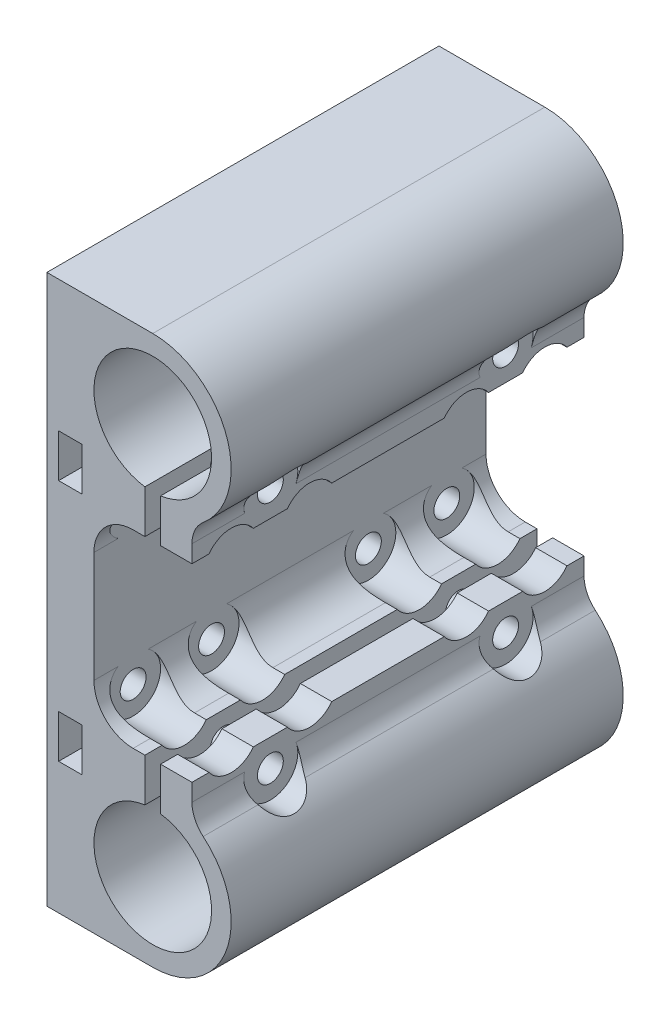
SolidWorks part; units mm, degrees
ref_plane "Plano frontal" through (0, 0, 0) normal (0, 0, 1) x (1, 0, 0)
ref_plane "Plano superior" through (0, 0, 0) normal (0, 1, 0) x (1, 0, 0)
ref_plane "Plano direito" through (0, 0, 0) normal (1, 0, 0) x (0, 0, -1)
sketch "Esboço1" plane through (0, 0, 0) normal (0, 0, 1) x (1, 0, 0)
  line L0 (0, 0) -> (67.7245, 0) construction
  line L1 (0, 35) -> (0, -35)
  line L2 (0, -35) -> (13.5, -35)
  line L3 (18.5, 14.2762) -> (18.5, 12.067)
  line L4 (18.5, 12.067) -> (14.5, 12.067)
  line L5 (12.5, -12.067) -> (11, -12.067)
  line L6 (6, -7.067) -> (6, 7.067)
  line L7 (12.5, -17.567) -> (12.5, -12.067)
  line L8 (14.5, 12.067) -> (14.5, 17.567)
  line L9 (12.5, 17.567) -> (12.5, 12.067)
  line L10 (13.5, 35) -> (0, 35)
  line L11 (12.5, 12.067) -> (11, 12.067)
  line L12 (14.5, -12.067) -> (14.5, -17.567)
  line L13 (18.5, -12.067) -> (14.5, -12.067)
  line L14 (18.5, -14.2762) -> (18.5, -12.067)
  line L15 (13.5, 25) -> (13.5, 21.6715) construction
  line L16 (4.5, -18.25) -> (1.5, -12.75) construction
  line L17 (4.5, 12.75) -> (1.5, 12.75)
  line L18 (4.5, 12.75) -> (4.5, 18.25)
  line L19 (4.5, 18.25) -> (1.5, 18.25)
  line L20 (1.5, 12.75) -> (1.5, 18.25)
  line L21 (4.5, 12.75) -> (1.5, 18.25) construction
  line L22 (4.5, 18.25) -> (1.5, 12.75) construction
  line L23 (4.5, -12.75) -> (1.5, -18.25) construction
  line L24 (1.5, -12.75) -> (1.5, -18.25)
  line L25 (4.5, -18.25) -> (1.5, -18.25)
  line L26 (4.5, -12.75) -> (4.5, -18.25)
  line L27 (4.5, -12.75) -> (1.5, -12.75)
  arc A0 (14.5, 17.567) -> (12.5, 17.567) centre (13.5, 25) ccw
  arc A1 (19.9286, -17.3401) -> (13.5, -35) centre (13.5, -25) cw
  arc A2 (19.9286, 17.3401) -> (13.5, 35) centre (13.5, 25) ccw
  arc A3 (14.5, -17.567) -> (12.5, -17.567) centre (13.5, -25) cw
  arc A4 (19.9286, -17.3401) -> (18.5, -14.2762) centre (22.5, -14.2762) cw
  arc A5 (18.5, 14.2762) -> (19.9286, 17.3401) centre (22.5, 14.2762) cw
  arc A6 (11, -12.067) -> (6, -7.067) centre (11, -7.067) cw
  arc A7 (11, 12.067) -> (6, 7.067) centre (11, 7.067) ccw
  point P3 (0, 0)
  point P28 (18.5, -16.3397)
  point P31 (18.5, 16.3397)
  point P32 (3, 15.5)
  point P42 (3, -15.5)
  point P46 (6, -12.067)
  point P49 (6, 12.067)
  dimension "D1" = 15
  dimension "D2" = 5.5
  dimension "D5" = 10
  dimension "D8" = 4
  dimension "D13" = 5
  dimension "D3" = 6
  dimension "D4" = 70
  dimension "D6" = 2
  dimension "D7" = 4
  dimension "D9" = 9.5
  dimension "D10" = 5.5
  dimension "D11" = 3
  dimension "D12" = 3
extrude "Ressalto-extrusão1" add sketch "Esboço1" along normal blind 50
sketch "Esboço6" plane through (14.5, 0, 0) normal (-1, 0, 0) x (0, 0, 1)
  line L1 (25, 35) -> (25, 0) construction
  line L2 (50, 35) -> (0, 35) construction
  line L3 (25, 0) -> (0, 0) construction
  line L4 (0, 32.5) -> (0, 17.567) construction
  line L6 (0, 25.0335) -> (50, 25.0335) construction
  line L7 (50, 17.567) -> (50, 32.5) construction
  circle A0 centre (10, 15.5335) radius 1.65
  circle A1 centre (40, 15.5335) radius 1.65
  circle A2 centre (40, -15.5335) radius 1.65
  circle A3 centre (10, -15.5335) radius 1.65
  dimension "D1" = 3.3
  dimension "D2" = 10
  dimension "D3" = 9.5
extrude "Corte-extrusão3" cut sketch "Esboço6" against normal through all both and the other way through all
sketch "Esboço7" plane through (18.5, 0, 0) normal (1, 0, 0) x (0, 0, -1)
  circle A0 centre (-40, 15.5335) radius 3.5
  circle A1 centre (-10, 15.5335) radius 3.5
  circle A2 centre (-10, -15.5335) radius 3.5
  circle A3 centre (-40, -15.5335) radius 3.5
  dimension "D1" = 7
extrude "Corte-extrusão4" cut sketch "Esboço7" along normal blind 10
sketch "Esboço9" plane through (6, 0, 0) normal (1, 0, 0) x (0, 0, -1)
  line L0 (-50, 0) -> (0, 0) construction
  line L1 (-50, -7.067) -> (-50, 7.067) construction
  line L2 (-25, 37.8538) -> (-25, -38.3217) construction
  circle A0 centre (-45, 10) radius 1.65
  circle A1 centre (-35, 10) radius 1.65
  circle A2 centre (-15, 10) radius 1.65
  circle A3 centre (-5, 10) radius 1.65
  circle A4 centre (-5, -10) radius 1.65
  circle A5 centre (-15, -10) radius 1.65
  circle A6 centre (-35, -10) radius 1.65
  circle A7 centre (-45, -10) radius 1.65
  point P9 (-25, 0)
  point P12 (0, 0)
  dimension "D2" = 3.3
  dimension "D1" = 20
  dimension "D3" = 40
  dimension "D4" = 20
extrude "Corte-extrusão6" cut sketch "Esboço9" against normal through all both and the other way through all
sketch "Esboço10" plane through (6, 0, 0) normal (1, 0, 0) x (0, 0, -1)
  circle A0 centre (-45, -10) radius 1.65 construction
  circle A1 centre (-35, -10) radius 1.65 construction
  circle A2 centre (-15, -10) radius 1.65 construction
  circle A3 centre (-5, -10) radius 1.65 construction
  circle A4 centre (-5, 10) radius 1.65 construction
  circle A5 centre (-15, 10) radius 1.65 construction
  circle A6 centre (-35, 10) radius 1.65 construction
  circle A7 centre (-45, 10) radius 1.65 construction
  circle A8 centre (-45, -10) radius 1.65
  circle A9 centre (-35, -10) radius 1.65
  circle A10 centre (-15, -10) radius 1.65
  circle A11 centre (-5, -10) radius 1.65
  circle A12 centre (-5, 10) radius 1.65
  circle A13 centre (-15, 10) radius 1.65
  circle A14 centre (-35, 10) radius 1.65
  circle A15 centre (-45, 10) radius 1.65
  circle A16 centre (-45, 10) radius 3.5
  circle A17 centre (-35, 10) radius 3.5
  circle A18 centre (-15, 10) radius 3.5
  circle A19 centre (-5, 10) radius 3.5
  circle A20 centre (-5, -10) radius 3.5
  circle A21 centre (-15, -10) radius 3.5
  circle A22 centre (-35, -10) radius 3.5
  circle A23 centre (-45, -10) radius 3.5
  dimension "D1" = 7
extrude "Corte-extrusão7" cut sketch "Esboço10" along normal through all
